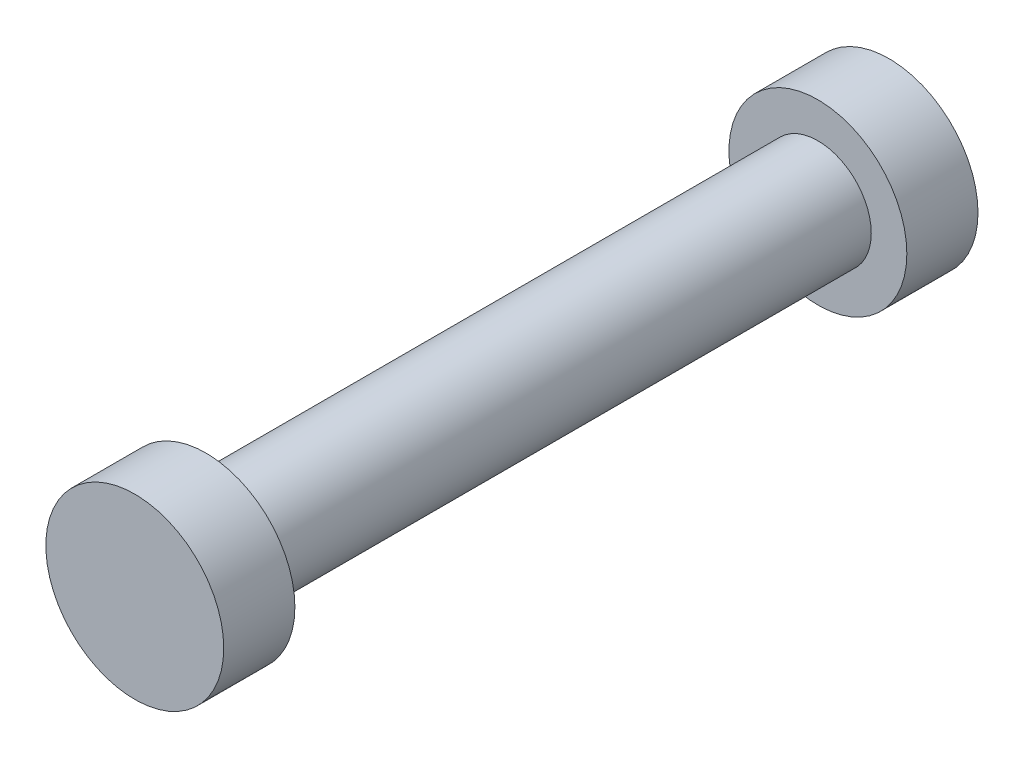
SolidWorks part; units mm, degrees
ref_plane "Front Plane" through (0, 0, 0) normal (0, 0, 1) x (1, 0, 0)
ref_plane "Top Plane" through (0, 0, 0) normal (0, 1, 0) x (1, 0, 0)
ref_plane "Right Plane" through (0, 0, 0) normal (1, 0, 0) x (0, 0, -1)
sketch "Sketch1" plane through (0, 0, 0) normal (0, 0, 1) x (1, 0, 0)
  circle A0 centre (0, 0) radius 12.5
  dimension "D1" = 25
extrude "Boss-Extrude1" add sketch "Sketch1" along normal blind 10
sketch "Sketch2" plane through (0, 0, 10) normal (0, 0, 1) x (1, 0, 0)
  circle A0 centre (0, 0) radius 7.5
  dimension "D1" = 15
extrude "Boss-Extrude2" add sketch "Sketch2" along normal blind 86
ref_plane "Plane1" through (0, -12.5, 0) normal (0, 1, 0) x (1, 0, 0)
sketch "Sketch4" plane through (0, 0, 96) normal (0, 0, 1) x (1, 0, 0)
  circle A0 centre (0, 0) radius 12.5
extrude "Boss-Extrude3" add sketch "Sketch4" along normal blind 10
